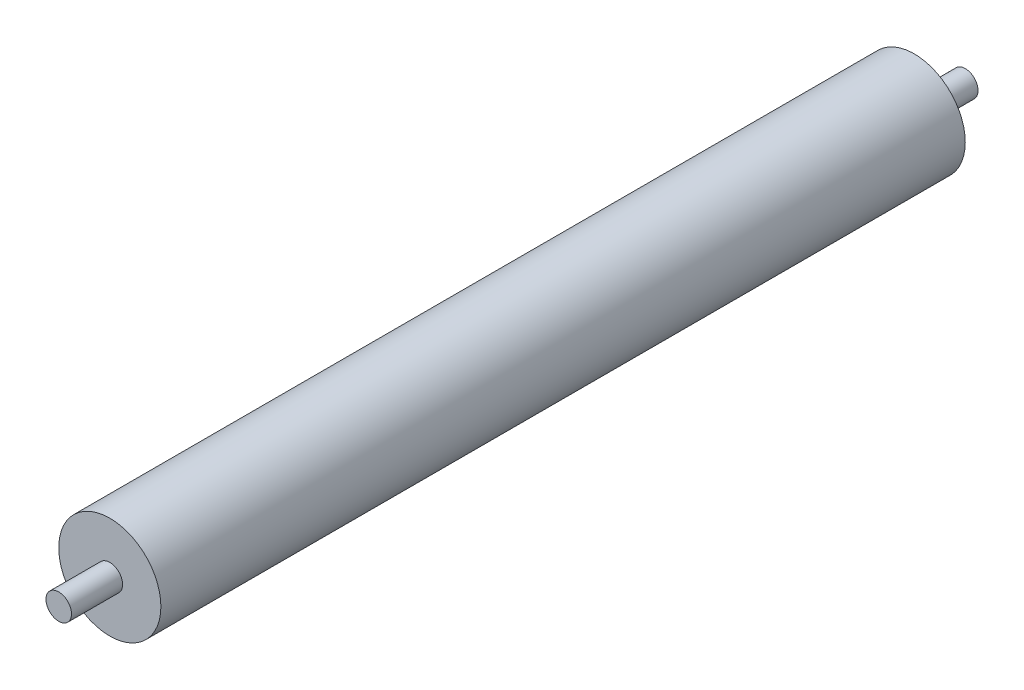
SolidWorks part; units mm, degrees
ref_plane "Front Plane" through (0, 0, 0) normal (0, 0, 1) x (1, 0, 0)
ref_plane "Top Plane" through (0, 0, 0) normal (0, 1, 0) x (1, 0, 0)
ref_plane "Right Plane" through (0, 0, 0) normal (1, 0, 0) x (0, 0, -1)
sketch "Sketch1" plane through (0, 0, 0) normal (0, 0, 1) x (1, 0, 0)
  circle A0 centre (0, 0) radius 20
  dimension "D1" = 40
extrude "Boss-Extrude1" add sketch "Sketch1" along normal blind 315
sketch "Sketch2" plane through (0, 0, 315) normal (0, 0, 1) x (1, 0, 0)
  circle A0 centre (0, 0) radius 5
  dimension "D1" = 10
extrude "Boss-Extrude2" add sketch "Sketch2" along normal blind 20
sketch "Sketch3" plane through (0, 0, 0) normal (0, 0, -1) x (-1, 0, 0)
  circle A0 centre (0, 0) radius 5
  dimension "D1" = 10
extrude "Boss-Extrude3" add sketch "Sketch3" along normal blind 20
